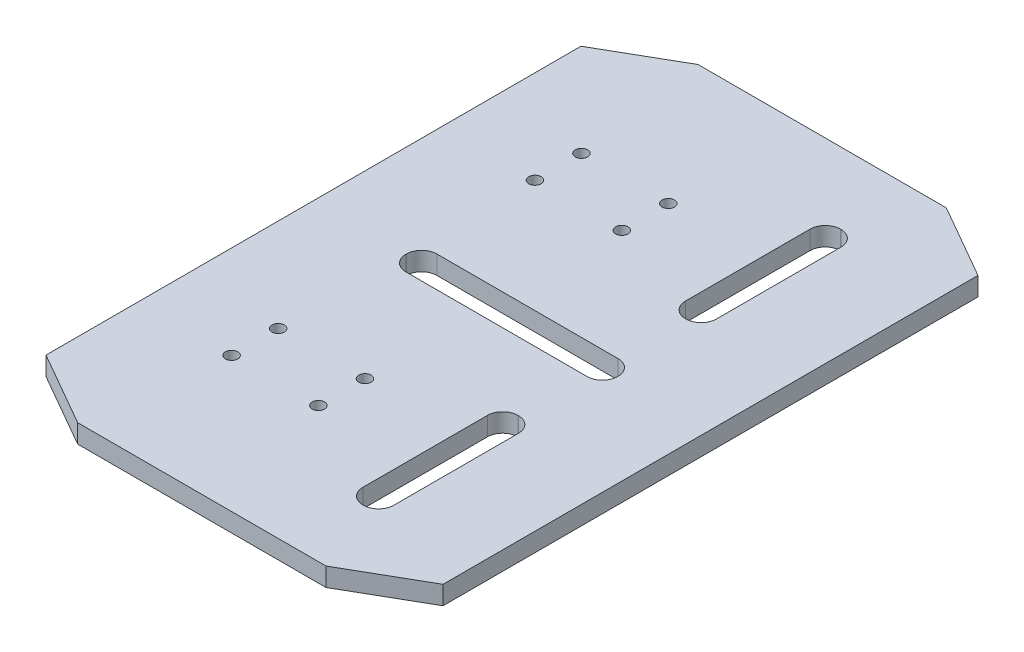
SolidWorks part; units mm, degrees
material "Custom Plastic"
ref_plane "Front Plane" through (0, 0, 0) normal (0, 0, 1) x (1, 0, 0)
ref_plane "Top Plane" through (0, 0, 0) normal (0, 1, 0) x (1, 0, 0)
ref_plane "Right Plane" through (0, 0, 0) normal (1, 0, 0) x (0, 0, -1)
sketch "Sketch1" plane through (0, 0, 0) normal (0, 1, 0) x (1, 0, 0)
  line L0 (-32, -43.1177) -> (-20.0119, -50)
  line L1 (-20.0119, -50) -> (20.0119, -50)
  line L2 (-32, -43.1177) -> (-32, 43.1177)
  line L3 (-20.0119, 50) -> (20.0119, 50)
  line L4 (32, -43.1177) -> (32, 43.1177)
  line L5 (-28.8545, -44.9235) -> (28.8545, 44.9235) construction
  line L6 (-28.4421, 45.1603) -> (28.4421, -45.1603) construction
  line L7 (-114.8204, 0) -> (150.9847, 0) construction
  line L8 (0, -72.5189) -> (0, 84.1411) construction
  line L9 (32, -43.1177) -> (20.0119, -50)
  line L10 (32, 43.1177) -> (20.0119, 50)
  line L11 (-32, 43.1177) -> (-20.0119, 50)
  point P0 (0, 0)
  dimension "D1" = 64
  dimension "D2" = 100
extrude "Boss-Extrude1" add sketch "Sketch1" along normal blind 3
sketch "Sketch5" plane through (0, 3, 0) normal (0, 1, 0) x (1, 0, 0)
  line L0 (-100.8141, 0) -> (111.641, 0) construction
  line L1 (14.5, 50) -> (14.5, -50) construction
  line L2 (-14.6202, -2.5) -> (14.6202, -2.5)
  line L3 (-17.0702, -0.05) -> (-17.0702, 0.05)
  line L4 (-14.6202, 2.5) -> (14.6202, 2.5)
  line L5 (17.0702, -0.05) -> (17.0702, 0.05)
  line L6 (-17.0702, -2.5) -> (17.0702, 2.5) construction
  line L7 (-17.0702, 2.5) -> (17.0702, -2.5) construction
  line L8 (20.0119, 50) -> (-20.0119, 50) construction
  line L9 (-20.0119, -50) -> (20.0119, -50) construction
  line L10 (14.5, 50) -> (14.5, 0) construction
  line L11 (14.5, 0) -> (14.5, -50) construction
  line L12 (14.45, -38.5) -> (14.55, -38.5)
  line L13 (14.45, 13.5) -> (14.55, 13.5)
  line L14 (12, 15.95) -> (12, 36.05)
  line L15 (14.45, 38.5) -> (14.55, 38.5)
  line L16 (17, 15.95) -> (17, 36.05)
  line L17 (12, 13.5) -> (17, 38.5) construction
  line L18 (12, 38.5) -> (17, 13.5) construction
  line L19 (12, -15.95) -> (12, -36.05)
  line L20 (14.45, -13.5) -> (14.55, -13.5)
  line L21 (17, -15.95) -> (17, -36.05)
  line L22 (32, -43.1177) -> (32, 43.1177) construction
  arc A0 (14.45, -38.5) -> (12, -36.05) centre (14.45, -36.05) cw
  arc A1 (14.55, -38.5) -> (17, -36.05) centre (14.55, -36.05) ccw
  arc A2 (12, -15.95) -> (14.45, -13.5) centre (14.45, -15.95) cw
  arc A3 (14.55, -13.5) -> (17, -15.95) centre (14.55, -15.95) cw
  arc A4 (-14.6202, -2.5) -> (-17.0702, -0.05) centre (-14.6202, -0.05) cw
  arc A5 (-17.0702, 0.05) -> (-14.6202, 2.5) centre (-14.6202, 0.05) cw
  arc A6 (14.6202, 2.5) -> (17.0702, 0.05) centre (14.6202, 0.05) cw
  arc A7 (14.6202, -2.5) -> (17.0702, -0.05) centre (14.6202, -0.05) ccw
  arc A8 (14.55, 13.5) -> (17, 15.95) centre (14.55, 15.95) ccw
  arc A9 (14.45, 13.5) -> (12, 15.95) centre (14.45, 15.95) cw
  arc A10 (12, 36.05) -> (14.45, 38.5) centre (14.45, 36.05) cw
  arc A11 (14.55, 38.5) -> (17, 36.05) centre (14.55, 36.05) cw
  point P3 (0, 0)
  point P14 (14.5, 0)
  point P15 (14.5, 26)
  point P17 (14.5, -26)
  point P18 (14.5, 26)
  point P31 (12, -38.5)
  point P34 (17, -38.5)
  point P37 (12, -13.5)
  point P40 (17, -13.5)
  dimension "D7" = 2.45
  dimension "D1" = 5
  dimension "D2" = 26
  dimension "D3" = 26
  dimension "D4" = 5
  dimension "D5" = 25
  dimension "D6" = 15
extrude "Cut-Extrude2" cut sketch "Sketch5" against normal blind 10
sketch "Sketch7" plane through (0, 3, 0) normal (0, 1, 0) x (1, 0, 0)
  line L0 (20.0119, 50) -> (-20.0119, 50) construction
  line L4 (-24, 17.035) -> (-24, 35.535)
  line L5 (4, 17.035) -> (-24, 17.035)
  line L6 (4, 35.535) -> (-24, 35.535)
  line L7 (4, 17.035) -> (4, 35.535)
  line L9 (-24, 31.95) -> (3.7524, 31.95)
  line L10 (-23.7676, 24.45) -> (4.2324, 24.45)
  line L11 (-10, 43.5449) -> (-10, 10.5144) construction
  line L12 (-17, 43.5449) -> (-17, 10.5144) construction
  line L14 (-23.7676, 28.2) -> (4, 28.2) construction
  line L16 (-32, 43.1177) -> (-32, -43.1177) construction
  circle A0 centre (-17, 28.2) radius 1
  circle A1 centre (-3, 28.2) radius 1
  circle A2 centre (-17, 20.7) radius 1
  circle A3 centre (-3, 20.7) radius 1
  point P12 (-16.7676, 25.035)
  point P17 (-17, 28.2)
  dimension "D5" = 2
  dimension "D1" = 7.5
  dimension "D2" = 7
  dimension "D3" = 14
  dimension "D4" = 3.75
  dimension "D6" = 28
  dimension "D7" = 8
  dimension "D8" = 14
  dimension "D9" = 14
  dimension "D10" = 7.5
  dimension "D11" = 7.5
  dimension "D12" = 7
  dimension "D13" = 21.8
ref_plane "Plane1" through (0, 0, 0) normal (0, 0, -1) x (-1, 0, 0)
extrude "Cut-Extrude3" cut sketch "Sketch7" against normal blind 11.5 contours A1 | A3 | A2 | A0
ref_plane "Plane2" through (0, 0, 0) normal (0, 0, -1) x (-1, 0, 0)
mirror "Mirror1" about plane through (0, 0, 0) normal (0, 0, -1) of "Cut-Extrude3"
